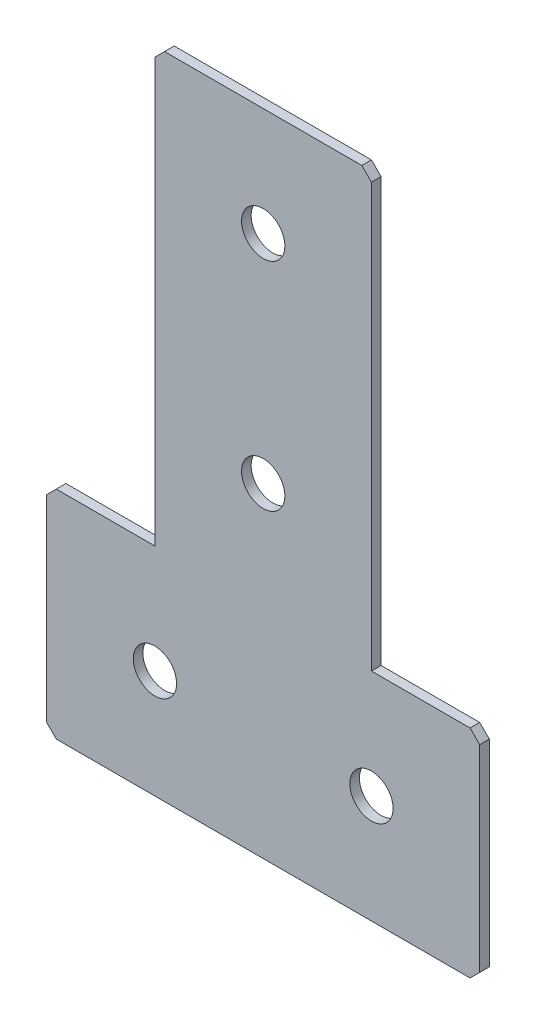
SolidWorks part; units mm, degrees
material "Простая углеродистая сталь"
ref_plane "Спереди(Плоскость XY)" through (0, 0, 0) normal (0, 0, 1) x (1, 0, 0)
ref_plane "Сверху(Плоскость XZ)" through (0, 0, 0) normal (0, 1, 0) x (1, 0, 0)
ref_plane "Справа(Плоскость ZY)" through (0, 0, 0) normal (1, 0, 0) x (0, 0, -1)
sketch "Эскиз1" plane through (0, 0, 0) normal (0, 0, -1) x (1, 0, 0)
  line L0 (0, 0) -> (0, 135) construction
  line L1 (-45, 135) -> (45, 135)
  line L2 (45, 135) -> (45, 90)
  line L3 (45, 90) -> (22.5, 90)
  line L4 (22.5, 90) -> (22.5, 0)
  line L5 (22.5, 0) -> (-22.5, 0)
  line L6 (-45, 135) -> (-45, 90)
  line L7 (-45, 90) -> (-22.5, 90)
  line L8 (-22.5, 90) -> (-22.5, 0)
  line L10 (-45, 112.5) -> (45, 112.5) construction
  dimension "D1" = 135
  dimension "D2" = 90
  dimension "D3" = 45
extrude "Бобышка-Вытянуть1" add sketch "Эскиз1" along normal blind 2
hole_wizard "Отверстие с зазором M81" positions "Эскиз2" profile "Эскиз3" hole size "M8" standard "DIN" end condition through all
sketch "Эскиз2" plane through (0, 0, -2) normal (0, 0, -1) x (1, 0, 0)
  line L6 (0, 0) -> (0, 112.5) construction
  line L12 (-22.5, 112.5) -> (22.5, 112.5) construction
  line L14 (22.5, 112.5) -> (45, 112.5) construction
  line L15 (45, 90) -> (45, 135) construction
  line L17 (-22.5, 0) -> (22.5, 0) construction
  point P40 (-22.5, 112.5)
  point P42 (22.5, 112.5)
  point P44 (0, 67.5)
  point P46 (0, 22.5)
  dimension "D1" = 45
  dimension "D2" = 22.5
  dimension "D3" = 45
sketch "Эскиз3" plane through (0, -22.5, -2) normal (1, 0, 0) x (0, 1, 0)
  line L0 (0, 0) -> (0, 2)
  line L1 (0, 2) -> (4.5, 2)
  line L2 (4.5, 2) -> (4.5, 0)
  line L5 (4.5, 0) -> (0, 0)
  line L11 (0, -6.35) -> (0, 107.95) construction
  dimension "Диаметр сквозного отверстия" = 9
  dimension "Глубина сквозного отверстия" = 2
chamfer "Фаска1" distance 2 angle 45 6 edges at (22.5, 0, -1) (45, -90, -1) (45, -135, -1) (-45, -135, -1) (-45, -90, -1) (-22.5, 0, -1)
